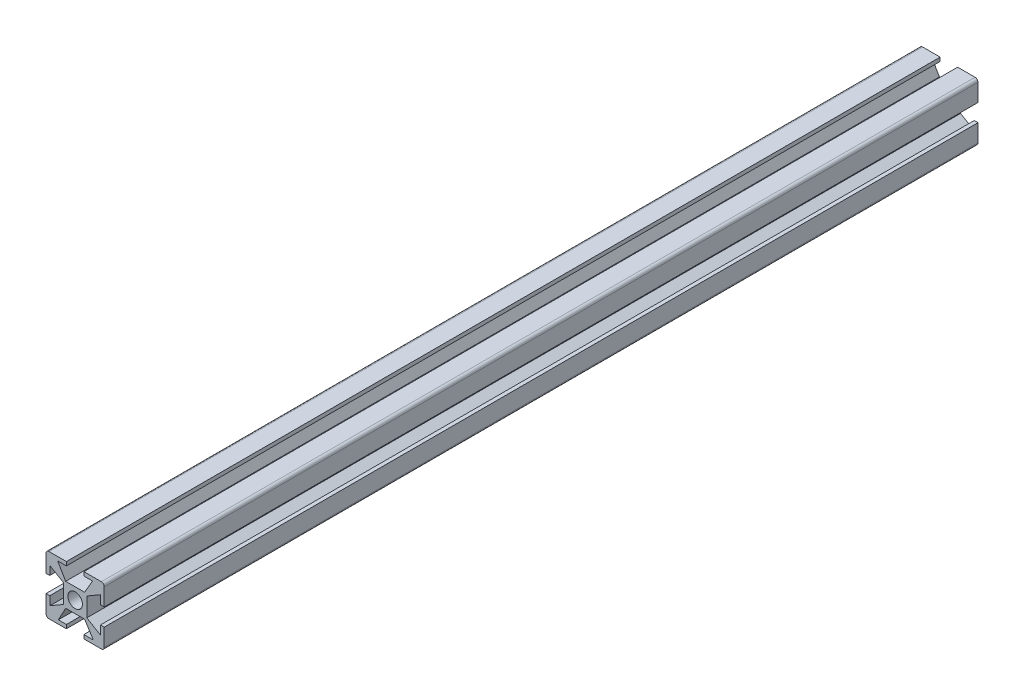
SolidWorks part; units mm, degrees
ref_plane "Alzado" through (0, 0, 0) normal (0, 0, 1) x (1, 0, 0)
ref_plane "Planta" through (0, 0, 0) normal (0, 1, 0) x (1, 0, 0)
ref_plane "Vista lateral" through (0, 0, 0) normal (1, 0, 0) x (0, 0, -1)
sketch "Croquis1" plane through (0, 0, 0) normal (0, 0, 1) x (1, 0, 0)
  line L0 (-3, 10) -> (3, 10)
  line L1 (-9, 10) -> (9, 10)
  line L2 (-10, 9) -> (-10, -9)
  line L3 (-9, -10) -> (9, -10)
  line L4 (10, 9) -> (10, -9)
  line L5 (-10, 10) -> (10, -10) construction
  line L6 (-10, -10) -> (10, 10) construction
  line L7 (-4, 4) -> (4, 4)
  line L8 (-4, 4) -> (-4, -4)
  line L9 (-4, -4) -> (4, -4)
  line L10 (4, 4) -> (4, -4)
  line L11 (-4, 4) -> (4, -4) construction
  line L12 (-4, -4) -> (4, 4) construction
  line L13 (3, 10) -> (3, 8.7)
  line L14 (-3.25, 4) -> (3.25, 4)
  line L15 (0, 10) -> (0, -10) construction
  line L16 (-10, 0) -> (10, 0) construction
  line L20 (-3, 10) -> (-3, 8.7)
  line L22 (3, -10) -> (3, -8.7)
  line L23 (-3, -10) -> (3, -10)
  line L24 (-3, -10) -> (-3, -8.7)
  line L25 (-5.75, -8.7) -> (-3, -8.7)
  line L26 (-5.75, -8.7) -> (-3.25, -4)
  line L27 (-3.25, -4) -> (3.25, -4)
  line L28 (6.25, -8.7) -> (3.25, -4)
  line L29 (3, -8.7) -> (6.25, -8.7)
  line L30 (-10, 3) -> (-10, -3)
  line L31 (-4, 3.25) -> (-4, -3.25)
  line L32 (-10, 3) -> (-8.7, 3)
  line L33 (-8.7, -6) -> (-8.7, -3)
  line L34 (-8.7, 6) -> (-4, 3.25)
  line L35 (-8.7, -6) -> (-4, -3.25)
  line L36 (-10, -3) -> (-8.7, -3)
  line L37 (-8.7, 3) -> (-8.7, 6)
  line L38 (8.7, -6) -> (4, -3.25)
  line L39 (4, 3.25) -> (4, -3.25)
  line L40 (8.7, 6) -> (4, 3.25)
  line L41 (8.7, 3) -> (8.7, 6)
  line L42 (10, 3) -> (8.7, 3)
  line L43 (10, 3) -> (10, -3)
  line L44 (10, -3) -> (8.7, -3)
  line L45 (8.7, -6) -> (8.7, -3)
  line L46 (-6, 8.7) -> (-3, 8.7)
  line L47 (-6, 8.7) -> (-3.25, 4)
  line L48 (6, 8.7) -> (3.25, 4)
  line L49 (3, 8.7) -> (6, 8.7)
  circle A0 centre (0, 0) radius 2.5
  arc A1 (-10, -9) -> (-9, -10) centre (-9, -9) ccw
  arc A2 (9, -10) -> (10, -9) centre (9, -9) ccw
  arc A3 (9, 10) -> (10, 9) centre (9, 9) cw
  arc A4 (-9, 10) -> (-10, 9) centre (-9, 9) ccw
  point P0 (0, 0)
  point P6 (0, 0)
  point P14 (0, 10)
  point P18 (0, 4)
  point P25 (0, 8.7)
  point P37 (-10, 0)
  point P40 (-4, 0)
  point P44 (-8.7, 0)
  point P56 (0, 8.7)
  dimension "D12" = 5
  dimension "D13" = 1
  dimension "D1" = 20
  dimension "D2" = 20
  dimension "D3" = 8
  dimension "D4" = 8
  dimension "D5" = 6
  dimension "D6" = 6.5
  dimension "D7" = 12
  dimension "D8" = 6.5
  dimension "D9" = 6
  dimension "D10" = 1.3
  dimension "D11" = 12
extrude "Saliente-Extruir4" add sketch "Croquis1" along normal blind 300 contours L1 A4 L2 L32 L37 L34 L8 L7 L47 L46 L20 | A3 L1 L13 L49 L48 L7 L10 L40 L41 L42 L4 | L3 A2 L4 L44 L45 L38 L10 L9 L28 L29 L22 | L2 A1 L3 L24 L25 L26 L9 L8 L35 L33 L36 | L10 L7 L8 L9 A0
